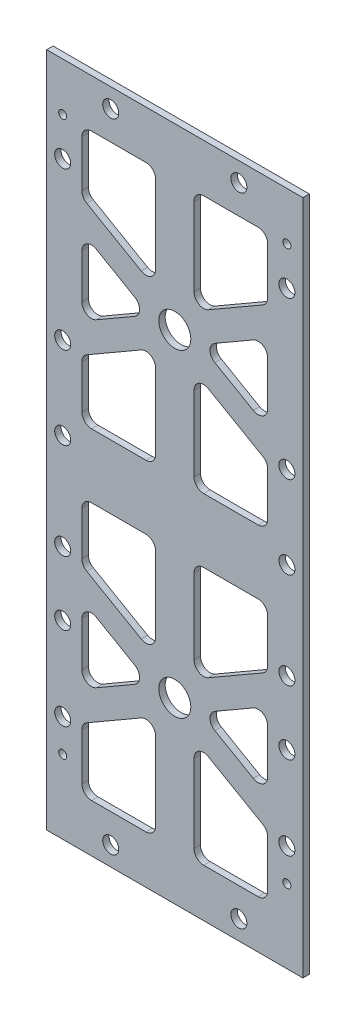
SolidWorks part; units mm, degrees
material "6061-T6 (SS)"
ref_plane "Front Plane" through (0, 0, 0) normal (0, 0, 1) x (1, 0, 0)
ref_plane "Top Plane" through (0, 0, 0) normal (0, 1, 0) x (1, 0, 0)
ref_plane "Right Plane" through (0, 0, 0) normal (1, 0, 0) x (0, 0, -1)
sketch "Sketch1" plane through (0, 0, 0) normal (0, 0, 1) x (1, 0, 0)
  line L1 (0, 0) -> (88, 0)
  line L2 (0, 0) -> (0, 211)
  line L3 (0, 211) -> (88, 211)
  line L4 (88, 0) -> (88, 211)
  dimension "D1" = 88
  dimension "D2" = 211
extrude "Boss-Extrude1" add sketch "Sketch1" along normal blind 2
sketch "Sketch2" plane through (0, 0, 2) normal (0, 0, 1) x (1, 0, 0)
  line L0 (0, 105.5) -> (88, 105.5) construction
  line L1 (0, 211) -> (0, 0) construction
  line L2 (88, 0) -> (88, 211) construction
  line L3 (44, 211) -> (44, 0) construction
  line L4 (88, 211) -> (0, 211) construction
  line L5 (0, 0) -> (88, 0) construction
  line L6 (0, 155.25) -> (88, 155.25) construction
  line L7 (0, 55.75) -> (88, 55.75) construction
  dimension "D1" = 55.75
  dimension "D2" = 55.75
sketch "Sketch3" plane through (0, 0, 2) normal (0, 0, 1) x (1, 0, 0)
  line L0 (0, 155.25) -> (88, 155.25) construction
  line L1 (38, 196) -> (38, 115.5)
  line L2 (0, 211) -> (0, 0) construction
  line L3 (15, 196) -> (73, 196)
  line L4 (15, 196) -> (15, 115.5)
  line L5 (15, 115.5) -> (73, 115.5)
  line L6 (73, 196) -> (73, 115.5)
  line L7 (88, 211) -> (0, 211) construction
  line L8 (88, 0) -> (88, 211) construction
  line L9 (0, 105.5) -> (88, 105.5) construction
  line L13 (73, 171.9932) -> (15, 138.5068) construction
  line L14 (15, 171.9932) -> (73, 138.5068) construction
  line L15 (73, 176.612) -> (15, 143.1256)
  line L16 (73, 167.3744) -> (15, 133.888)
  line L17 (15, 176.612) -> (73, 143.1256)
  line L18 (15, 167.3744) -> (73, 133.888)
  line L19 (50, 196) -> (50, 115.5)
  circle A0 centre (44, 155.25) radius 5
  dimension "D1" = 10
  dimension "D3" = 15
  dimension "D4" = 15
  dimension "D5" = 15
  dimension "D6" = 10
  dimension "D9" = 30
  dimension "D10" = 30
  dimension "D11" = 8
  dimension "D12" = 4
  dimension "D13" = 4
  dimension "D14" = 8
ref_plane "Plane1" through (0, 105.5, 0) normal (0, 1, 0) x (1, 0, 0)
extrude "Cut-Extrude2" cut sketch "Sketch3" against normal blind 2
sketch "Sketch4" plane through (0, 0, 2) normal (0, 0, 1) x (1, 0, 0)
  line L0 (0, 155.25) -> (88, 155.25) construction
  circle A0 centre (44, 155.25) radius 5
  dimension "D1" = 10
extrude "Cut-Extrude3" cut sketch "Sketch4" against normal through all
mirror "Mirror2" about plane through (0, 105.5, 0) normal (0, 1, 0) of "Cut-Extrude2", "Cut-Extrude3"
fillet "Fillet2" radius 3 44 edges at (73, 67.8744, 1) (73, 43.6256, 1) (52, 55.75, 1) (15, 15, 1) (15, 34.388, 1) (15, 143.1256, 1) (15, 167.3744, 1) (36, 155.25, 1) (15, 115.5, 1) (15, 133.888, 1) (73, 196, 1) (73, 115.5, 1) (73, 133.888, 1) (15, 196, 1) (15, 176.612, 1) (73, 167.3744, 1) (73, 143.1256, 1) (52, 155.25, 1) (73, 95.5, 1) (73, 77.112, 1) (73, 34.388, 1) (73, 15, 1) (15, 77.112, 1) (15, 95.5, 1) (15, 43.6256, 1) (15, 67.8744, 1) (36, 55.75, 1) (73, 176.612, 1) (50, 15, 1) (38, 15, 1) (38, 47.6671, 1) (50, 47.6671, 1) (38, 63.8329, 1) (38, 95.5, 1) (50, 63.8329, 1) (50, 95.5, 1) (38, 115.5, 1) (38, 147.1671, 1) (50, 147.1671, 1) (50, 115.5, 1) (38, 196, 1) (38, 163.3329, 1) (50, 163.3329, 1) (50, 196, 1)
sketch "Sketch23" plane through (0, 0, 2) normal (0, 0, 1) x (1, 0, 0)
  line L2 (88, 211) -> (88, 0)
  line L3 (86, 211) -> (86, 0)
  line L4 (86, 211) -> (88, 211)
  line L5 (86, 0) -> (88, 0)
  line L6 (2.1504, 211) -> (2.1504, 0)
  line L7 (2.1504, 211) -> (0, 211)
  line L8 (0, 211) -> (0, 0)
  line L9 (2.1504, 0) -> (0, 0)
  dimension "D1" = 2
extrude "Cut-Extrude5" cut sketch "Sketch23" against normal blind 10 contours L5 L2 L4 L3 | L6 L9 L8 L7
sketch "Sketch29" plane through (0, 0, 0) normal (0, 0, -1) x (-1, 0, 0)
  line L0 (-44, 0) -> (-44, 211)
  line L4 (-86, 105.5) -> (-2.1504, 105.5)
  line L5 (-86, 0) -> (-86, 211) construction
  line L6 (-2.1504, 0) -> (-2.1504, 211) construction
  line L16 (-4, 211) -> (1.9115, 211)
  line L17 (-4, 211) -> (-4, 0)
  line L18 (-4, 0) -> (1.9115, 0)
  line L19 (1.9115, 211) -> (1.9115, 0)
  line L20 (-84, 0) -> (-88.0365, 0)
  line L21 (-84, 0) -> (-84, 211)
  line L22 (-84, 211) -> (-88.0365, 211)
  line L23 (-88.0365, 0) -> (-88.0365, 211)
  point P0 (-44, 155.25)
  point P1 (-44, 217.1483)
  point P3 (-4, 155.25)
  point P4 (-4, 217.1483)
  point P5 (-84, 155.25)
  point P6 (-84, 217.1483)
  point P8 (-4, 105.5)
  point P22 (-84, 105.5)
  point P23 (-44, 105.5)
extrude "Cut-Extrude10" cut sketch "Sketch29" against normal blind 2
sketch "Sketch30" plane through (0, 0, 2) normal (0, 0, 1) x (1, 0, 0)
  line L0 (44, 211) -> (44, 0) construction
  line L1 (84, 211) -> (4, 211) construction
  line L2 (4, 0) -> (84, 0) construction
  line L3 (4, 211) -> (4, 0) construction
  point P8 (64, 6)
  point P9 (79, 23)
  point P10 (79, 33.2)
  point P11 (9, 33.2)
  point P13 (9, 196)
  point P14 (9, 184)
  point P15 (9, 135)
  point P16 (9, 109.2)
  point P18 (9, 79.2)
  point P19 (9, 59.2)
  point P20 (79, 59.2)
  point P21 (9, 23)
  point P23 (24, 205)
  point P25 (79, 79.2)
  point P26 (79, 109.2)
  point P27 (24, 6)
  point P29 (79, 135)
  point P30 (79, 184)
  point P31 (79, 196)
  point P32 (64, 205)
  dimension "D1" = 20
  dimension "D2" = 6
  dimension "D3" = 5
  dimension "D4" = 15
  dimension "D5" = 27
  dimension "D6" = 76
  dimension "D7" = 101.8
  dimension "D8" = 131.8
  dimension "D9" = 151.8
  dimension "D10" = 5
  dimension "D11" = 188
  dimension "D12" = 205
  dimension "D13" = 20
  dimension "D14" = 5
  dimension "D15" = 5
  dimension "D16" = 5
  dimension "D17" = 5
  dimension "D18" = 5
  dimension "D19" = 5
  dimension "D20" = 177.8
hole_wizard "Ø5.0mm Dowel Hole1" positions "Sketch31" profile "Sketch32" hole size "Ø5.0" standard "ANSI Metric" end condition through all
sketch "Sketch31" plane through (0, 0, 2) normal (0, 0, 1) x (1, 0, 0)
  point P0 (24, 205)
  point P3 (64, 205)
  point P6 (9, 184)
  point P9 (79, 184)
  point P12 (9, 135)
  point P15 (79, 135)
  point P18 (79, 109.2)
  point P21 (9, 109.2)
  point P24 (9, 79.2)
  point P27 (79, 79.2)
  point P30 (79, 59.2)
  point P33 (9, 59.2)
  point P36 (9, 33.2)
  point P39 (79, 33.2)
  point P42 (64, 6)
  point P45 (24, 6)
sketch "Sketch32" plane through (24, 205, 2) normal (1, 0, 0) x (0, -1, 0)
  line L0 (0, 0) -> (0, 2)
  line L1 (0, 2) -> (2.5, 2)
  line L2 (2.5, 2) -> (2.5, 0)
  line L5 (2.5, 0) -> (0, 0)
  line L11 (0, -6.35) -> (0, 107.95) construction
  dimension "Thru Hole Dia." = 5
  dimension "Thru Hole Depth" = 2
hole_wizard "Tap Drill for M3x0.5 Tap1" positions "Sketch33" profile "Sketch34" hole size "M3x0.5" standard "ANSI Metric" end condition through all
sketch "Sketch33" plane through (0, 0, 2) normal (0, 0, 1) x (1, 0, 0)
  point P0 (9, 23)
  point P3 (79, 23)
  point P6 (9, 196)
  point P9 (79, 196)
sketch "Sketch34" plane through (9, 23, 2) normal (1, 0, 0) x (0, -1, 0)
  line L0 (0, 0) -> (0, 2)
  line L1 (0, 2) -> (1.25, 2)
  line L2 (1.25, 2) -> (1.25, 0)
  line L5 (1.25, 0) -> (0, 0)
  line L11 (0, -6.35) -> (0, 107.95) construction
  dimension "Thru Hole Dia." = 2.5
  dimension "Thru Hole Depth" = 2
equation "\"stack_house_hole_distance\"=15"
equation "\"battery_top_clearance\"=15"
equation "\"coils_top_clearance\"=10"
